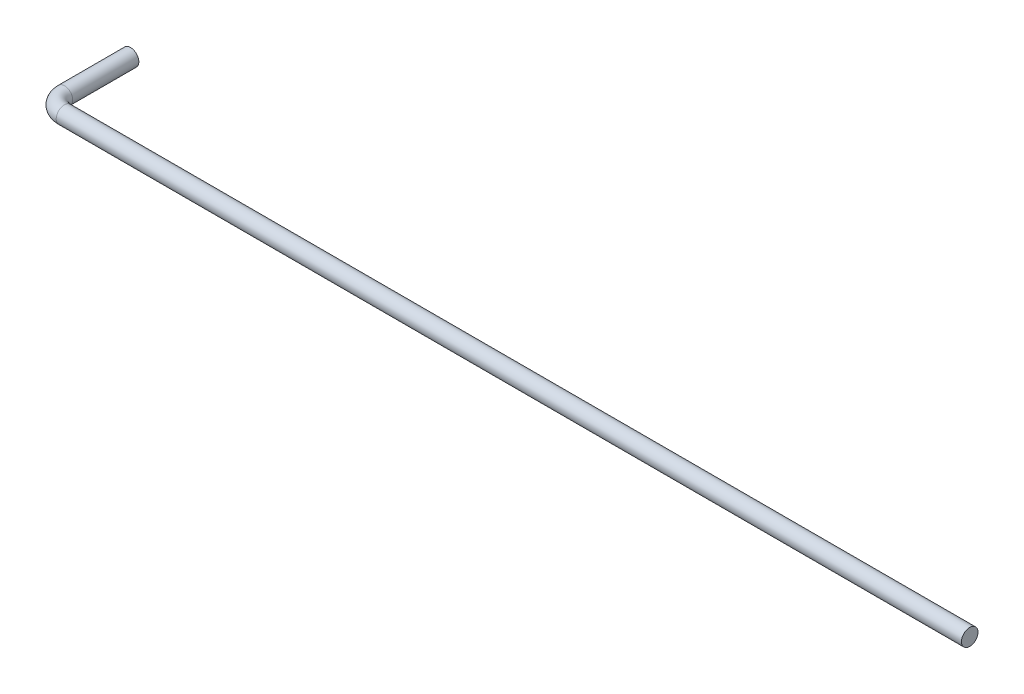
SolidWorks part; units mm, degrees
ref_plane "정면" through (0, 0, 0) normal (0, 0, 1) x (1, 0, 0)
ref_plane "윗면" through (0, 0, 0) normal (0, 1, 0) x (1, 0, 0)
ref_plane "우측면" through (0, 0, 0) normal (1, 0, 0) x (0, 0, -1)
sketch "스케치1" plane through (0, 0, 0) normal (0, 1, 0) x (1, 0, 0)
  line L0 (-54.4456, 0) -> (55.1144, 0)
  line L1 (-56.4456, 2) -> (-56.4456, 10)
  arc A0 (-56.4456, 2) -> (-54.4456, 0) centre (-54.4456, 2) ccw
  point P6 (-56.4456, 0)
  dimension "D3" = 2
  dimension "D1" = 111.56
  dimension "D2" = 10
sweep "스윕1" add path "스케치1" circular profile diameter 2 parameters "D3"=2
